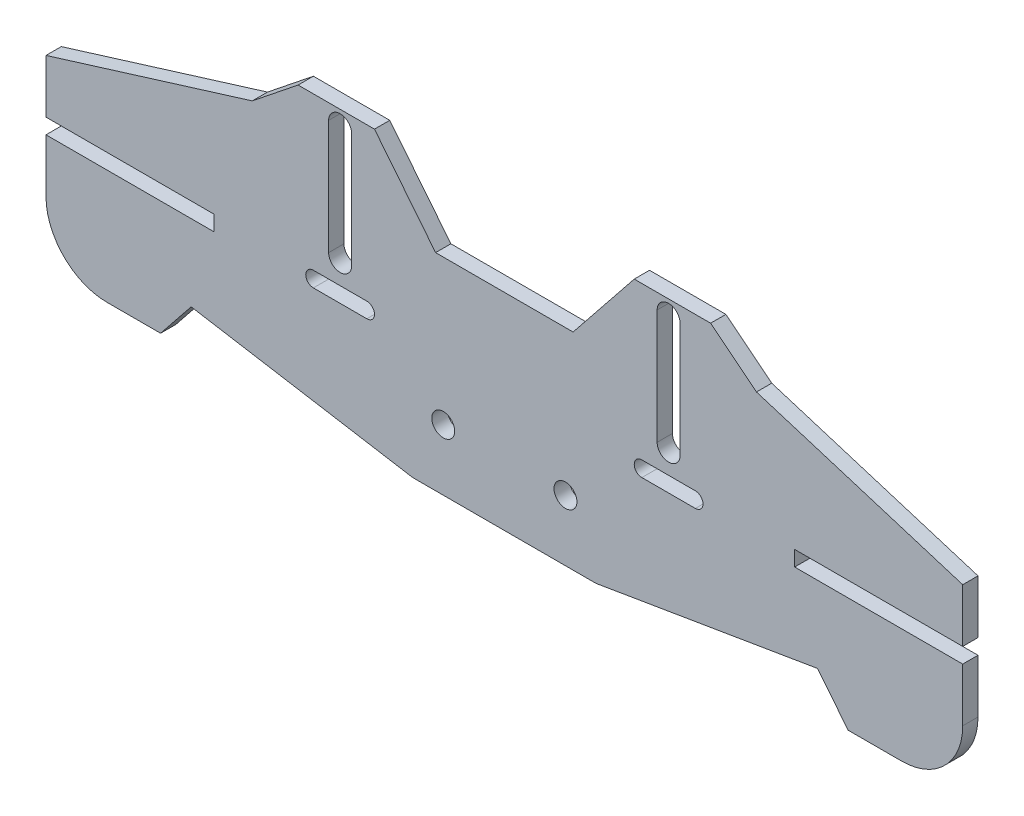
SolidWorks part; units mm, degrees
material "Plástico personalizado"
ref_plane "Plano frontal" through (0, 0, 0) normal (0, 0, 1) x (1, 0, 0)
ref_plane "Plano superior" through (0, 0, 0) normal (0, 1, 0) x (1, 0, 0)
ref_plane "Plano direito" through (0, 0, 0) normal (1, 0, 0) x (0, 0, -1)
sketch "Esboço1" plane through (0, 0, 0) normal (0, 0, 1) x (1, 0, 0)
  line L0 (52, -0.1434) -> (45, -0.1434)
  line L1 (0, 27) -> (9, 27)
  line L2 (9, 27) -> (17, 37)
  line L3 (17, 37) -> (27, 37)
  line L4 (27, 37) -> (33, 32.2)
  line L5 (33, 32.2) -> (60, 23.8566)
  line L6 (60, 23.8566) -> (60, 7.8566)
  line L7 (45, -0.1434) -> (41, 4.8566)
  line L8 (41, 4.8566) -> (12, 0)
  line L9 (0, 27) -> (0, 0)
  line L10 (12, 0) -> (0, 0)
  arc A0 (52, -0.1434) -> (60, 7.8566) centre (52, 7.8566) ccw
  point P11 (60, -0.1434)
  dimension "D14" = 8
  dimension "D1" = 27
  dimension "D2" = 9
  dimension "D3" = 12
  dimension "D4" = 10
  dimension "D5" = 10
  dimension "D6" = 8
  dimension "D7" = 6
  dimension "D8" = 15
  dimension "D9" = 29
  dimension "D10" = 24
  dimension "D11" = 4
  dimension "D12" = 5
  dimension "D15" = 27
extrude "Ressalto-extrusão1" add sketch "Esboço1" along normal blind 2
mirror "Espelhar1" about plane through (0, 0, 0) normal (1, 0, 0) of "Ressalto-extrusão1"
sketch "Esboço2" plane through (0, 0, 2) normal (0, 0, 1) x (1, 0, 0)
  line L0 (60, 7.8566) -> (60, 23.8566) construction
  line L1 (60, 14.8566) -> (38, 14.8566)
  line L2 (60, 14.8566) -> (60, 16.8566)
  line L3 (60, 16.8566) -> (38, 16.8566)
  line L4 (38, 14.8566) -> (38, 16.8566)
  line L5 (21.5, 35) -> (21.5, 20) construction
  line L6 (23, 35) -> (23, 20)
  line L7 (20, 35) -> (20, 20)
  line L8 (27, 37) -> (17, 37) construction
  line L9 (-12, 0) -> (12, 0) construction
  line L10 (25, 16) -> (18, 16) construction
  line L11 (25, 15) -> (18, 15)
  line L12 (25, 17) -> (18, 17)
  line L13 (0, -2.4631) -> (0, 35) construction
  line L14 (-21.5, 35) -> (-21.5, 20) construction
  line L15 (-23, 35) -> (-23, 20)
  line L16 (-20, 35) -> (-20, 20)
  line L17 (-25, 16) -> (-18, 16) construction
  line L18 (-25, 15) -> (-18, 15)
  line L19 (-25, 17) -> (-18, 17)
  line L20 (-38, 14.8566) -> (-38, 16.8566)
  line L21 (-60, 16.8566) -> (-38, 16.8566)
  line L22 (-60, 14.8566) -> (-60, 16.8566)
  line L23 (-60, 14.8566) -> (-38, 14.8566)
  arc A0 (23, 35) -> (20, 35) centre (21.5, 35) ccw
  arc A1 (20, 20) -> (23, 20) centre (21.5, 20) ccw
  circle A2 centre (8, 8) radius 1.5
  arc A3 (25, 15) -> (25, 17) centre (25, 16) ccw
  arc A4 (18, 17) -> (18, 15) centre (18, 16) ccw
  arc A5 (-23, 35) -> (-20, 35) centre (-21.5, 35) cw
  arc A6 (-20, 20) -> (-23, 20) centre (-21.5, 20) cw
  arc A7 (-25, 15) -> (-25, 17) centre (-25, 16) cw
  arc A8 (-18, 17) -> (-18, 15) centre (-18, 16) cw
  circle A9 centre (-8, 8) radius 1.5
  point P9 (21.5, 27.5)
  point P24 (21.5, 16)
  point P34 (-21.5, 27.5)
  point P41 (-21.5, 16)
  dimension "D7" = 3
  dimension "D1" = 22
  dimension "D2" = 7
  dimension "D3" = 2
  dimension "D4" = 2
  dimension "D5" = 3
  dimension "D6" = 4
  dimension "D8" = 8
  dimension "D9" = 4
  dimension "D10" = 7
  dimension "D11" = 13
  dimension "D12" = 1
  dimension "D13" = 20
  dimension "D14" = 15
extrude "Corte-extrusão1" cut sketch "Esboço2" against normal through all
